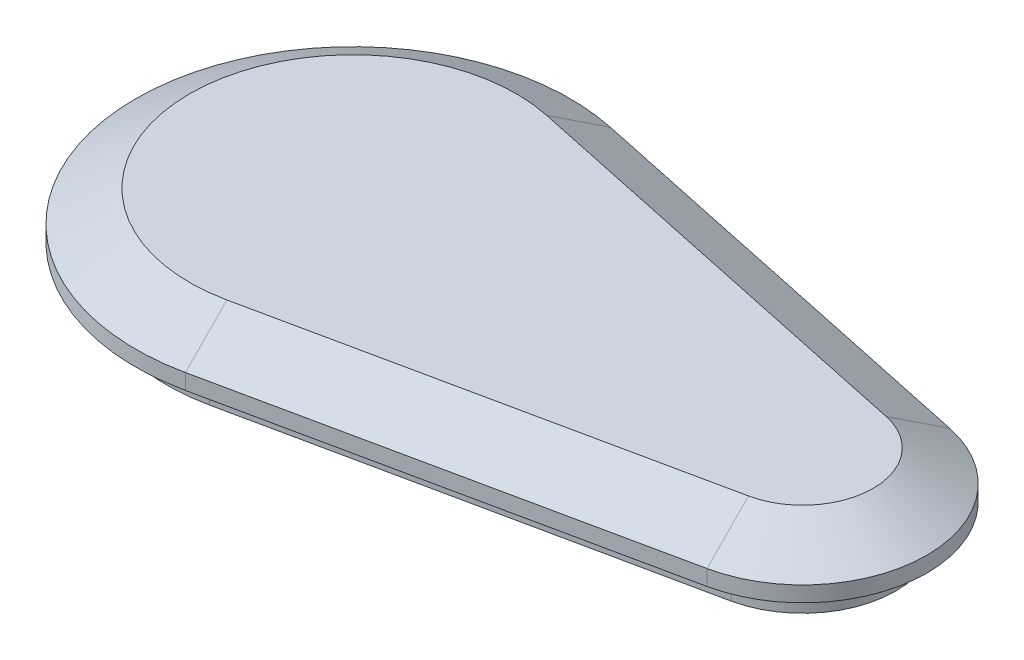
SolidWorks part; units mm, degrees
ref_plane "Front Plane" through (0, 0, 0) normal (0, 0, 1) x (1, 0, 0)
ref_plane "Top Plane" through (0, 0, 0) normal (0, 1, 0) x (1, 0, 0)
ref_plane "Right Plane" through (0, 0, 0) normal (1, 0, 0) x (0, 0, -1)
sketch "Sketch1" plane through (0, 0, 0) normal (0, 1, 0) x (1, 0, 0)
  line L0 (0, 0) -> (29, 0) construction
  line L1 (2.4828, 11.7404) -> (30.2414, 5.8702)
  line L2 (2.4828, -11.7404) -> (30.2414, -5.8702)
  arc A0 (2.4828, 11.7404) -> (2.4828, -11.7404) centre (0, 0) ccw
  arc A1 (30.2414, -5.8702) -> (30.2414, 5.8702) centre (29, 0) ccw
  point P1 (99.4327, 0)
  point P4 (103.0678, 0)
  point P6 (99.4327, 0)
  point P10 (63.4894, 0)
  dimension "D1" = 12
  dimension "D2" = 6
  dimension "D3" = 29
extrude "Boss-Extrude1" add sketch "Sketch1" along normal blind 2
sketch "Sketch2" plane through (0, 2, 0) normal (0, 1, 0) x (1, 0, 0)
  line L0 (30.6552, 7.8269) -> (2.8966, 13.6971)
  line L1 (2.8966, -13.6971) -> (30.6552, -7.8269)
  line L2 (2.4828, -11.7404) -> (30.2414, -5.8702)
  line L3 (30.2414, 5.8702) -> (2.4828, 11.7404)
  line L4 (2.4828, -11.7404) -> (30.2414, -5.8702) construction
  line L5 (30.2414, 5.8702) -> (2.4828, 11.7404) construction
  arc A0 (2.8966, 13.6971) -> (2.8966, -13.6971) centre (0, 0) ccw
  arc A1 (30.6552, -7.8269) -> (30.6552, 7.8269) centre (29, 0) ccw
  arc A2 (2.4828, 11.7404) -> (2.4828, -11.7404) centre (0, 0) ccw
  arc A3 (30.2414, -5.8702) -> (30.2414, 5.8702) centre (29, 0) ccw
  arc A4 (2.4828, 11.7404) -> (2.4828, -11.7404) centre (0, 0) ccw construction
  arc A5 (30.2414, -5.8702) -> (30.2414, 5.8702) centre (29, 0) ccw construction
  dimension "D1" = 0
  dimension "D2" = 2
extrude "Boss-Extrude2" add sketch "Sketch2" along normal blind 1
sketch "Sketch3" plane through (0, 3, 0) normal (0, 1, 0) x (1, 0, 0)
  line L2 (30.6552, 7.8269) -> (2.8966, 13.6971)
  line L3 (2.8966, -13.6971) -> (30.6552, -7.8269)
  line L4 (30.6552, 7.8269) -> (2.8966, 13.6971)
  line L5 (2.8966, -13.6971) -> (30.6552, -7.8269)
  arc A2 (30.6552, -7.8269) -> (30.6552, 7.8269) centre (29, 0) ccw
  arc A3 (2.8966, 13.6971) -> (2.8966, -13.6971) centre (0, 0) ccw
  arc A4 (30.6552, -7.8269) -> (30.6552, 7.8269) centre (29, 0) ccw
  arc A5 (2.8966, 13.6971) -> (2.8966, -13.6971) centre (0, 0) ccw
  dimension "D1" = 0
extrude "Boss-Extrude3" add sketch "Sketch3" along normal blind 2 draft 60
